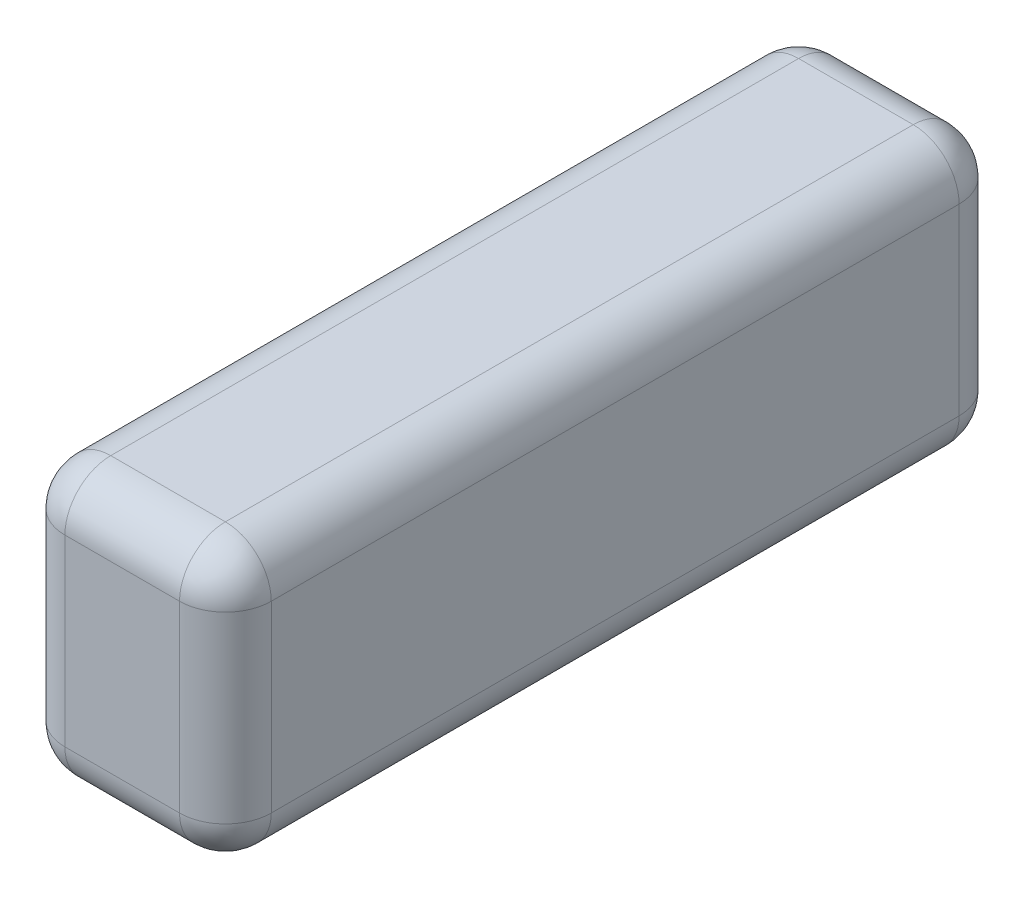
SolidWorks part; units mm, degrees
ref_plane "Face" through (0, 0, 0) normal (0, 0, 1) x (1, 0, 0)
ref_plane "Dessus" through (0, 0, 0) normal (0, 1, 0) x (1, 0, 0)
ref_plane "Droite" through (0, 0, 0) normal (1, 0, 0) x (0, 0, -1)
sketch "Esquisse1" plane through (0, 0, 0) normal (0, 0, 1) x (1, 0, 0)
  line L1 (0, 0) -> (45, 0)
  line L2 (0, 0) -> (0, 60)
  line L3 (0, 60) -> (45, 60)
  line L4 (45, 0) -> (45, 60)
  dimension "D1" = 45
  dimension "D2" = 60
extrude "Boss.-Extru.1" add sketch "Esquisse1" along normal blind 170
fillet "Congé1" radius 10 12 edges at (45, 30, 0) (45, 60, 85) (0, 60, 85) (22.5, 60, 0) (0, 0, 85) (45, 0, 85) (22.5, 0, 0) (22.5, 60, 170) (45, 30, 170) (22.5, 0, 170) (0, 30, 170) (0, 30, 0)
